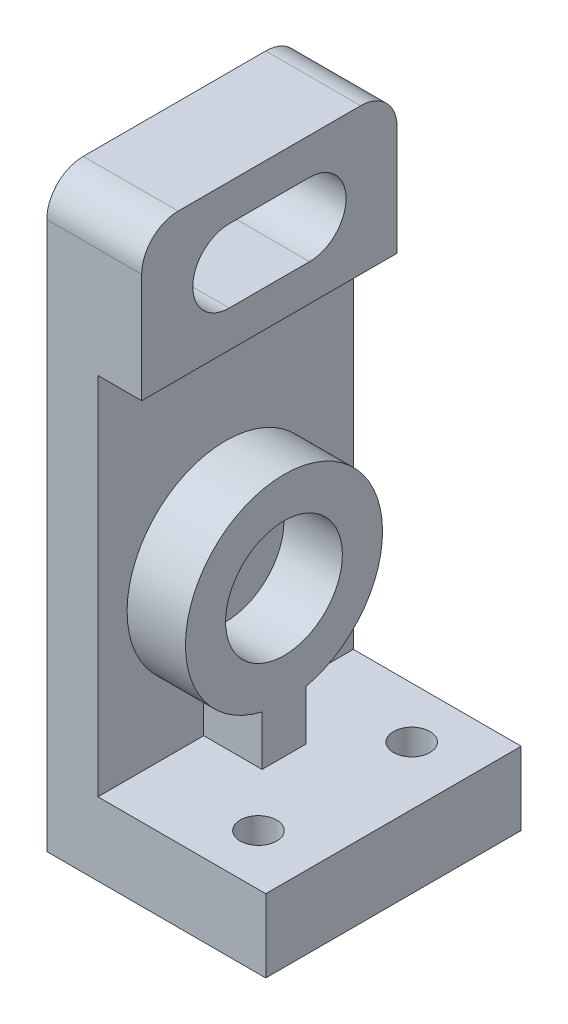
SolidWorks part; units mm, degrees
ref_plane "Ön Düzlem" through (0, 0, 0) normal (0, 0, 1) x (1, 0, 0)
ref_plane "Üst Düzlem" through (0, 0, 0) normal (0, 1, 0) x (1, 0, 0)
ref_plane "Sağ Düzlem" through (0, 0, 0) normal (1, 0, 0) x (0, 0, -1)
sketch "Çizim1" plane through (0, 0, 0) normal (0, 1, 0) x (1, 0, 0)
  line L1 (-15, 17.5) -> (15, 17.5)
  line L2 (-15, 17.5) -> (-15, -17.5)
  line L3 (-15, -17.5) -> (15, -17.5)
  line L4 (15, 17.5) -> (15, -17.5)
  line L5 (-15, 17.5) -> (15, -17.5) construction
  line L6 (-15, -17.5) -> (15, 17.5) construction
  point P0 (0, 0)
  dimension "D1" = 35
  dimension "D2" = 30
extrude "Yükseklik-Ekstrüzyon1" add sketch "Çizim1" along normal blind 10
sketch "Çizim2" plane through (0, 10, 0) normal (0, 1, 0) x (1, 0, 0)
  line L0 (15, 17.5) -> (-15, 17.5) construction
  line L1 (-15, -17.5) -> (-8, -17.5)
  line L2 (-15, -17.5) -> (-15, 17.5)
  line L3 (-15, 17.5) -> (-8, 17.5)
  line L4 (-8, -17.5) -> (-8, 17.5)
  dimension "D1" = 7
extrude "Yükseklik-Ekstrüzyon2" add sketch "Çizim2" along normal blind 70
sketch "Çizim3" plane through (-8, 0, 0) normal (1, 0, 0) x (0, 0, -1)
  line L0 (17.5, 80) -> (17.5, 10) construction
  line L1 (-17.5, 80) -> (17.5, 80)
  line L2 (-17.5, 80) -> (-17.5, 60)
  line L3 (-17.5, 60) -> (17.5, 60)
  line L4 (17.5, 80) -> (17.5, 60)
  dimension "D1" = 20
extrude "Yükseklik-Ekstrüzyon3" add sketch "Çizim3" along normal blind 6
fillet "Radyus1" radius 5 2 edges at (-8.5, 80, -17.5) (-8.5, 80, 17.5)
sketch "Çizim4" plane through (-2, 0, 0) normal (1, 0, 0) x (0, 0, -1)
  line L0 (-5.5, 70) -> (5.5, 70) construction
  line L1 (-5.5, 75) -> (5.5, 75)
  line L2 (-5.5, 65) -> (5.5, 65)
  arc A0 (-5.5, 75) -> (-5.5, 65) centre (-5.5, 70) ccw
  arc A1 (5.5, 65) -> (5.5, 75) centre (5.5, 70) ccw
  point P2 (0, 70)
  point P7 (0, 0)
  dimension "D1" = 10
  dimension "D2" = 70
  dimension "D3" = 11
extrude "Kes-Ekstrüzyon1" cut sketch "Çizim4" against normal through all
sketch "Çizim5" plane through (0, 10, 0) normal (0, 1, 0) x (1, 0, 0)
  line L0 (15, -17.5) -> (15, 17.5) construction
  line L1 (-8, -17.5) -> (15, -17.5) construction
  circle A0 centre (7, 10.5) radius 2.5
  circle A1 centre (7, -10.5) radius 2.5
  point P4 (0, 0)
  dimension "D2" = 5
  dimension "D3" = 5
  dimension "D1" = 8
  dimension "D4" = 7
  dimension "D5" = 21
extrude "Kes-Ekstrüzyon2" cut sketch "Çizim5" against normal through all
sketch "Çizim6" plane through (-8, 0, 0) normal (1, 0, 0) x (0, 0, -1)
  line L0 (-17.5, 10) -> (17.5, 10) construction
  line L2 (-3, 10) -> (3, 10)
  line L3 (-3, 10) -> (-3, 16.8376)
  line L5 (3, 10) -> (3, 16.8376)
  circle A0 centre (0, 30) radius 8
  arc A1 (3, 16.8376) -> (-3, 16.8376) centre (0, 30) ccw
  point P5 (0, 10)
  dimension "D1" = 16
  dimension "D2" = 27
  dimension "D3" = 20
  dimension "D4" = 6
extrude "Yükseklik-Ekstrüzyon4" add sketch "Çizim6" along normal blind 8
